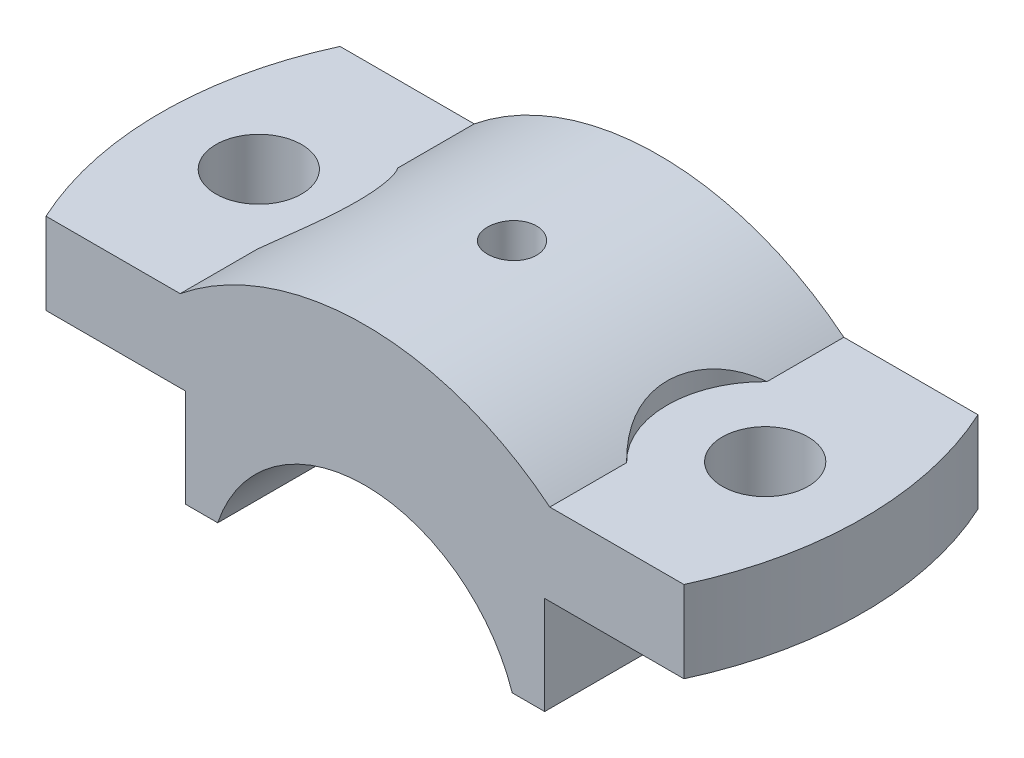
SolidWorks part; units mm, degrees
ref_plane "Front Plane" through (0, 0, 0) normal (0, 0, 1) x (1, 0, 0)
ref_plane "Top Plane" through (0, 0, 0) normal (0, 1, 0) x (1, 0, 0)
ref_plane "Right Plane" through (0, 0, 0) normal (1, 0, 0) x (0, 0, -1)
sketch "Sketch1" plane through (0, 0, 0) normal (0, 0, 1) x (1, 0, 0)
  line L0 (0, 31.3374) -> (0, 11.2263) construction
  line L1 (-22.6274, 20.2263) -> (-43, 20.2263)
  line L2 (-43, 20.2263) -> (-43, 10.2263)
  line L3 (-43, 10.2263) -> (-22, 10.2263)
  line L4 (-22, 10.2263) -> (-22, -1.7737)
  line L5 (0, 28.2263) -> (-35.5351, 28.2263) construction
  line L7 (22, 10.2263) -> (22, -1.7737)
  line L8 (43, 10.2263) -> (22, 10.2263)
  line L9 (43, 20.2263) -> (43, 10.2263)
  line L10 (22.6274, 20.2263) -> (43, 20.2263)
  line L11 (-22, -1.7737) -> (-18.0278, -1.7737)
  line L12 (18.0278, -1.7737) -> (22, -1.7737)
  arc A0 (-18.0278, -1.7737) -> (18.0278, -1.7737) centre (0, -7.7737) cw
  arc A1 (-22.6274, 20.2263) -> (22.6274, 20.2263) centre (0, -7.7737) cw
  dimension "D3" = 19
  dimension "D4" = 36
  dimension "D1" = 10
  dimension "D2" = 22
  dimension "D5" = 43
  dimension "D6" = 43
  dimension "D7" = 12
  dimension "D8" = 6
  dimension "D9" = 8
extrude "Boss-Extrude1" add sketch "Sketch1" along normal blind 36 contours L1 L2 L3 L4 L11 A0 L12 L7 L8 L9 L10 A1
sketch "Sketch3" plane through (0, 20.2263, 0) normal (0, 1, 0) x (1, 0, 0)
  line L0 (-39.0512, 0) -> (39.0512, 0)
  line L1 (-22.6274, 0) -> (-43, 0) construction
  line L2 (22.6274, 0) -> (43, 0) construction
  line L3 (-39.0512, -36) -> (39.0512, -36)
  line L4 (22.6274, -36) -> (43, -36) construction
  line L5 (-39.0512, 0) -> (-43, 0)
  line L6 (-43, 0) -> (-43, -18)
  arc A0 (-39.0512, 0) -> (-39.0512, -36) centre (0, -18) ccw
  arc A1 (39.0512, -36) -> (39.0512, 0) centre (0, -18) ccw
  point P0 (0, -18)
extrude "Cut-Extrude1" cut sketch "Sketch3" against normal blind 10 contours A0 L5 L6
sketch "Sketch4" plane through (0, 20.2263, 0) normal (0, 1, 0) x (1, 0, 0)
  line L0 (-43, -18) -> (-43, -36)
  line L1 (-43, -36) -> (-39.0512, -36)
  line L2 (-22.6274, -36) -> (-43, -36) construction
  circle A0 centre (0, -18) radius 43
  point P0 (0, -18)
  line M2 (-43, -18) -> (-43, -36)
  line M3 (-43, -36) -> (-22.6274, -36)
extrude "Cut-Extrude2" cut sketch "Sketch4" against normal blind 10 contours A0 M2 M3
sketch "Sketch5" plane through (0, 20.2263, 0) normal (0, 1, 0) x (1, 0, 0)
  line L0 (-22.6274, -18) -> (90.0158, -18) construction
  line L2 (-22.6274, -36) -> (-22.6274, 0) construction
  line L3 (0, 0) -> (0, -59.9955) construction
  line L5 (43, -18) -> (43, 0)
  line L6 (43, 0) -> (39.0512, 0)
  line L9 (43, -18) -> (43, -36)
  line L10 (43, -36) -> (39.0512, -36)
  circle A0 centre (0, -18) radius 43
  point P0 (0.1429, -18.0656)
  line M1 (43, 0) -> (22.6274, 0)
  line M3 (22.6274, -36) -> (43, -36)
  line M4 (43, -36) -> (43, 0)
extrude "Cut-Extrude8" cut sketch "Sketch5" against normal blind 10 contours A0 M3 M4 | A0 M4 M1
sketch "Sketch9" plane through (0, 20.2263, 0) normal (0, 1, 0) x (1, 0, 0)
  line L0 (-43, -18) -> (43, -18) construction
  line L1 (0, 0) -> (0, -36) construction
  line L2 (-22.6274, -36) -> (22.6274, -36) construction
  arc A0 (-39.0512, 0) -> (-39.0512, -36) centre (0, -18) ccw construction
  arc A1 (39.0512, -36) -> (39.0512, 0) centre (0, -18) ccw construction
  circle A2 centre (31, -18) radius 5.25
  circle A3 centre (-31, -18) radius 5.25
  dimension "D2" = 10.5
  dimension "D1" = 31
extrude "Cut-Extrude9" cut sketch "Sketch9" against normal blind 10
sketch "Sketch10" plane through (0, 20.2263, 0) normal (0, 1, 0) x (1, 0, 0)
  line L0 (-43, -18) -> (43, -18) construction
  line L1 (22.6274, 0) -> (22.6274, -36)
  line L2 (22.6274, -9.4035) -> (22.6274, -26.5965)
  line L3 (0, 0) -> (0, -36) construction
  line L4 (-22.6274, -36) -> (22.6274, -36) construction
  line L5 (-22.6274, -9.4035) -> (-22.6274, -26.5965)
  arc A0 (-39.0512, 0) -> (-39.0512, -36) centre (0, -18) ccw construction
  arc A1 (39.0512, -36) -> (39.0512, 0) centre (0, -18) ccw construction
  arc A2 (-22.6274, -9.4035) -> (-22.6274, -26.5965) centre (-31, -18) cw
  arc A3 (22.6274, -9.4035) -> (22.6274, -26.5965) centre (31, -18) ccw
extrude "Cut-Extrude10" cut sketch "Sketch10" along normal blind 10 contours A2 L5 | A3 L2
ref_plane "Plane1" through (0, 28.2263, 0) normal (0, 1, 0) x (1, 0, 0)
sketch "Sketch11" plane through (0, 28.2263, 0) normal (0, 1, 0) x (1, 0, 0)
  line L0 (19, -18) -> (-19, -18) construction
  line L1 (0, 0) -> (0, -18) construction
  arc A0 (22.6274, -9.4035) -> (22.6274, -26.5965) centre (31, -18) ccw construction
  arc A1 (-22.6274, -26.5965) -> (-22.6274, -9.4035) centre (-31, -18) ccw construction
  circle A2 centre (0, -18) radius 3
  dimension "D1" = 6
extrude "Cut-Extrude11" cut sketch "Sketch11" against normal blind 10
sketch "Sketch13" plane through (0, 18.2263, 0) normal (0, 1, 0) x (1, 0, 0)
  circle A0 centre (0, -18) radius 1.5
  dimension "D1" = 3
extrude "Cut-Extrude12" cut sketch "Sketch13" against normal blind 10
fillet "Fillet2" radius 1 1 edges at (-3, 18.2263, 18)
